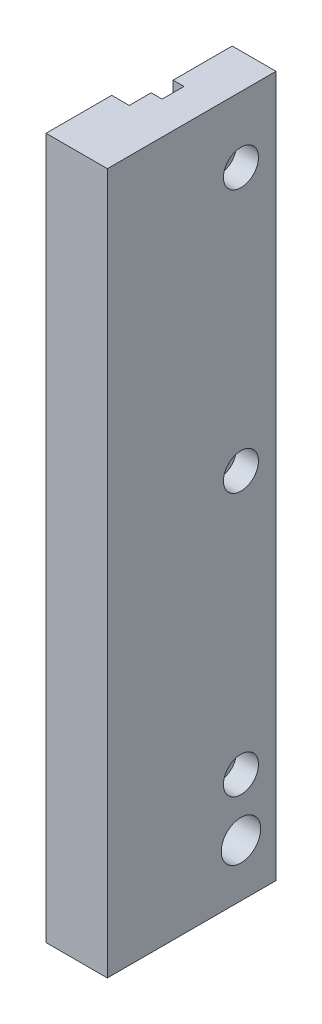
SolidWorks part; units mm, degrees
ref_plane "Front Plane" through (0, 0, 0) normal (0, 0, 1) x (1, 0, 0)
ref_plane "Top Plane" through (0, 0, 0) normal (0, 1, 0) x (1, 0, 0)
ref_plane "Right Plane" through (0, 0, 0) normal (1, 0, 0) x (0, 0, -1)
sketch "Sketch1" plane through (0, 0, 0) normal (0, 1, 0) x (1, 0, 0)
  line L1 (0, 20) -> (2.5, 20)
  line L2 (2.5, 20) -> (2.5, 25)
  line L3 (2.5, 25) -> (0, 25)
  line L4 (0, 25) -> (0, 38.5)
  line L5 (0, 38.5) -> (10, 38.5)
  line L6 (10, 38.5) -> (10, 0)
  line L7 (10, 0) -> (0, 0)
  line L8 (0, 20) -> (0, 15)
  line L9 (0, 15) -> (-4, 15)
  line L10 (-4, 15) -> (-4, 0)
  line L11 (-4, 0) -> (0, 0)
  dimension "D1" = 5
  dimension "D2" = 2.5
  dimension "D3" = 10
  dimension "D4" = 14
  dimension "D5" = 13.5
  dimension "D6" = 15
  dimension "D7" = 5
extrude "Boss-Extrude1" add sketch "Sketch1" along normal blind 160
sketch "Sketch2" plane through (10, 0, 0) normal (1, 0, 0) x (0, 0, -1)
  line L0 (38.5, 160) -> (38.5, 0) construction
  line L1 (0, 160) -> (38.5, 160) construction
  line L2 (0, 0) -> (38.5, 0) construction
  circle A0 centre (30.5, 145) radius 4
  circle A1 centre (30.5, 85) radius 4
  circle A2 centre (30.5, 25) radius 4
  circle A3 centre (30.5, 12) radius 4.5
  dimension "D1" = 8
  dimension "D6" = 9
  dimension "D2" = 8
  dimension "D3" = 60
  dimension "D4" = 60
  dimension "D5" = 12
  dimension "D7" = 15
extrude "Cut-Extrude2" cut sketch "Sketch2" against normal blind 5
sketch "Sketch3" plane through (5, 0, 0) normal (1, 0, 0) x (0, 0, -1)
  circle A0 centre (30.5, 145) radius 2.5
  circle A1 centre (30.5, 85) radius 2.5
  circle A2 centre (30.5, 25) radius 2.5
  circle A3 centre (30.5, 12) radius 4.5
  dimension "D1" = 5
  dimension "D2" = 9
extrude "Cut-Extrude3" cut sketch "Sketch3" against normal through all
